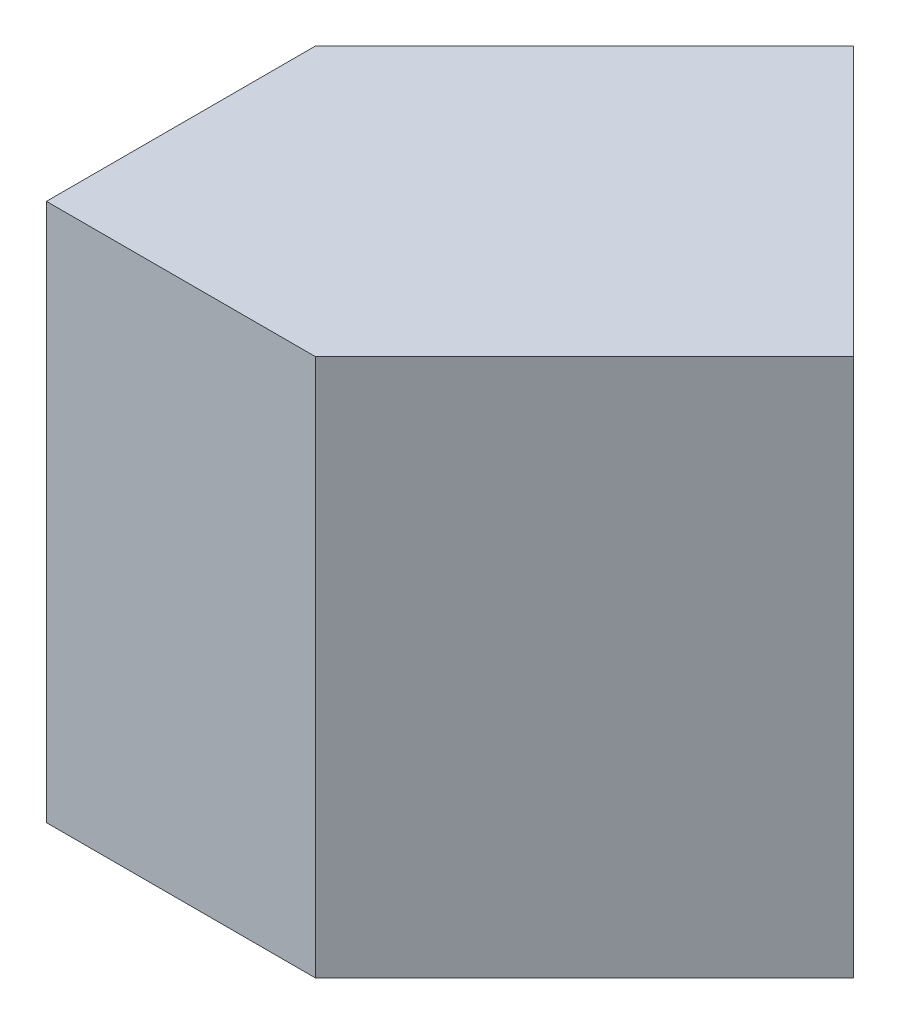
SolidWorks part; units mm, degrees
ref_plane "Front Plane" through (0, 0, 0) normal (0, 0, 1) x (1, 0, 0)
ref_plane "Top Plane" through (0, 0, 0) normal (0, 1, 0) x (1, 0, 0)
ref_plane "Right Plane" through (0, 0, 0) normal (1, 0, 0) x (0, 0, -1)
sketch "Sketch1" plane through (0, 0, 0) normal (0, 0, 1) x (1, 0, 0)
  line L1 (0, 0) -> (20, 0)
  line L2 (0, 0) -> (0, 20)
  line L3 (0, 20) -> (20, 20)
  line L4 (20, 0) -> (20, 20)
  dimension "D1" = 20
  dimension "D2" = 20
extrude "Boss-Extrude1" add sketch "Sketch1" along normal blind 20
sketch "Sketch2" plane through (0, 20, 0) normal (0, 1, 0) x (1, 0, 0)
  line L0 (20, 0) -> (10, 0)
  line L1 (20, 0) -> (0, 0) construction
  line L2 (10, 0) -> (20, -10)
  line L3 (20, -20) -> (20, 0) construction
  line L4 (20, -10) -> (20, 0)
extrude "Cut-Extrude1" cut sketch "Sketch2" against normal blind 20
sketch "Sketch3" plane through (0, 20, 0) normal (0, 1, 0) x (1, 0, 0)
  line L0 (20, -20) -> (20, -10)
  line L1 (20, -10) -> (10, -20)
  line L2 (20, -20) -> (0, -20) construction
  line L3 (10, -20) -> (20, -20)
extrude "Cut-Extrude2" cut sketch "Sketch3" against normal blind 20
sketch "Sketch4" plane through (0, 20, 0) normal (0, 1, 0) x (1, 0, 0)
  line L0 (0, 0) -> (10, 0)
  line L1 (10, 0) -> (0, -10)
  line L2 (0, -20) -> (0, 0) construction
  line L3 (0, -10) -> (0, 0)
extrude "Cut-Extrude3" cut sketch "Sketch4" against normal blind 20
